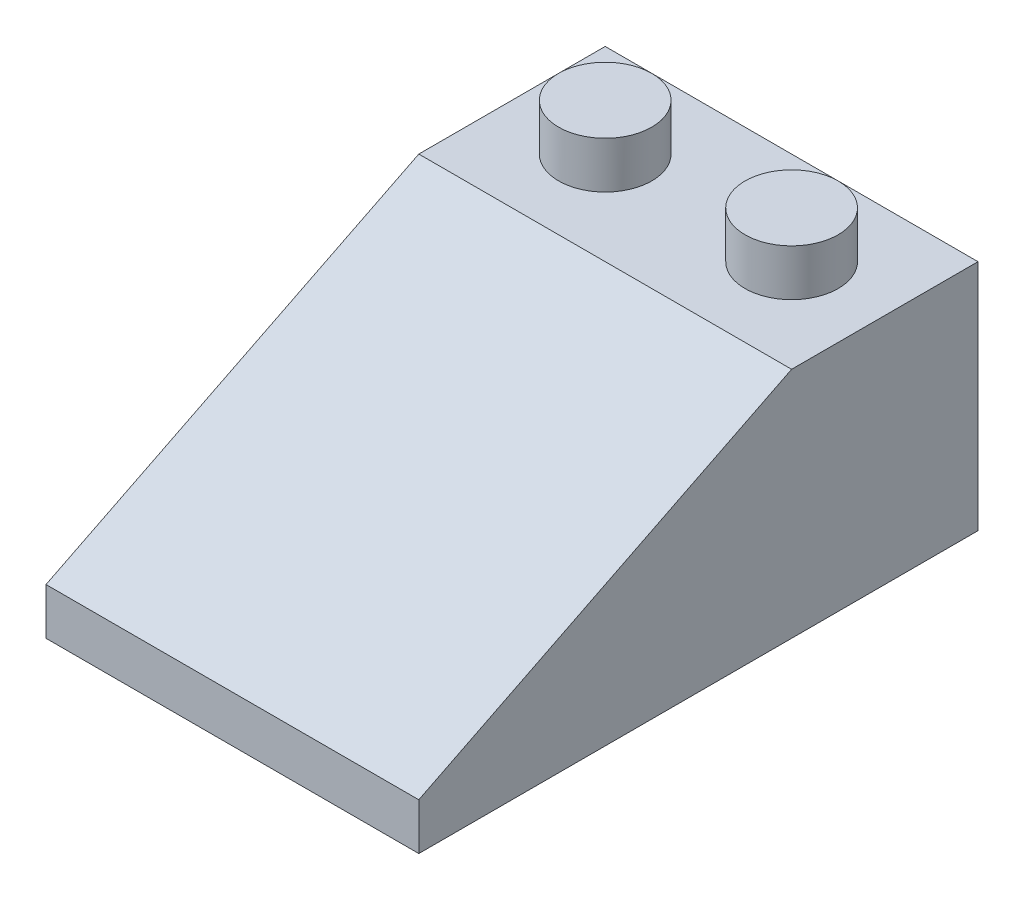
SolidWorks part; units mm, degrees
ref_plane "Front Plane" through (0, 0, 0) normal (0, 0, 1) x (1, 0, 0)
ref_plane "Top Plane" through (0, 0, 0) normal (0, 1, 0) x (1, 0, 0)
ref_plane "Right Plane" through (0, 0, 0) normal (1, 0, 0) x (0, 0, -1)
sketch "Sketch1" plane through (0, 0, 0) normal (1, 0, 0) x (0, 0, -1)
  line L0 (0, 0) -> (0, 10)
  line L1 (0, 10) -> (-8, 10)
  line L2 (-8, 10) -> (-24, 2)
  line L3 (-24, 2) -> (-24, 0)
  line L4 (-24, 0) -> (0, 0)
  dimension "D1" = 24
  dimension "D2" = 10
  dimension "D3" = 8
  dimension "D4" = 2
extrude "Boss-Extrude1" add sketch "Sketch1" along normal blind 16
sketch "Sketch2" plane through (0, 10, 0) normal (0, 1, 0) x (1, 0, 0)
  line L0 (8, 1.6172) -> (8, -8) construction
  line L1 (16, -8) -> (0, -8) construction
  line L2 (16, 0) -> (0, 0) construction
  line L3 (0, 0) -> (0, -8) construction
  circle A0 centre (4, -4) radius 2
  circle A1 centre (12, -4) radius 2
  dimension "D1" = 4
  dimension "D2" = 4
  dimension "D3" = 4
extrude "Boss-Extrude2" add sketch "Sketch2" along normal blind 2
shell "Shell1" thickness 1
sketch "Sketch3" plane through (0, 0, 0) normal (0, -1, 0) x (1, 0, 0)
  line L0 (8, 0) -> (8, 8) construction
  line L3 (16, 0) -> (0, 0) construction
  line L4 (1, 12) -> (15.2599, 12) construction
  line L5 (1, 23) -> (1, 1) construction
  circle A0 centre (8, 8) radius 2.7
  circle A1 centre (8, 8) radius 1.7
  circle A2 centre (8, 16) radius 1.7
  circle A3 centre (8, 16) radius 2.7
  dimension "D1" = 5.4
  dimension "D2" = 3.4
  dimension "D3" = 8
extrude "Boss-Extrude3" add sketch "Sketch3" against normal up to next
